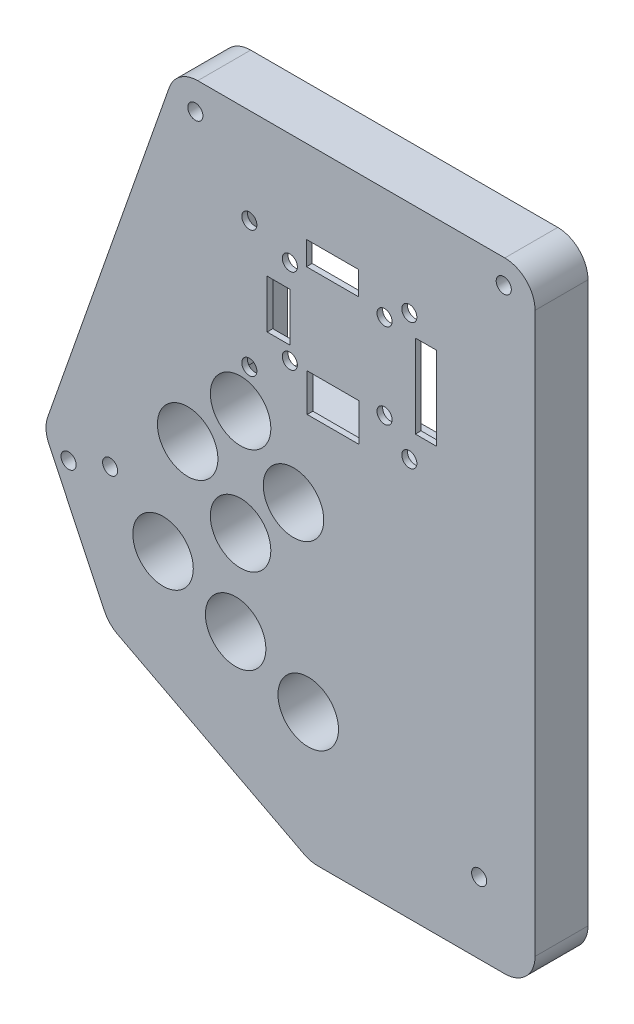
SolidWorks part; units mm, degrees
ref_plane "Front Plane" through (0, 0, 0) normal (0, 0, 1) x (1, 0, 0)
ref_plane "Top Plane" through (0, 0, 0) normal (0, 1, 0) x (1, 0, 0)
ref_plane "Right Plane" through (0, 0, 0) normal (1, 0, 0) x (0, 0, -1)
sketch "Sketch1" plane through (0, 0, 0) normal (0, 0, 1) x (1, 0, 0)
  line L6 (-20.066, -57.15) -> (46.99, -57.15) construction
  line L7 (-12.446, -73.152) -> (46.99, -73.152) construction
  line L8 (-3.3141, 6.35) -> (48.26, 6.35)
  line L9 (53.34, 1.27) -> (53.34, -92.71)
  line L10 (48.26, -97.79) -> (16.847, -97.79)
  line L16 (-8.1072, 2.9529) -> (-28.5162, -55.1739)
  line L18 (-20.066, -57.15) -> (-29.21, -57.15) construction
  line L26 (0, 0) -> (46.99, 0) construction
  line L27 (46.99, 0) -> (46.99, -88.9) construction
  line L28 (46.99, -88.9) -> (17.78, -88.9) construction
  line L29 (17.78, -88.9) -> (-12.446, -73.152) construction
  line L30 (-12.446, -73.152) -> (-20.066, -57.15) construction
  line L31 (-20.066, -57.15) -> (0, 0) construction
  line L32 (46.99, -57.15) -> (46.99, -88.9) construction
  line L33 (17.78, -88.9) -> (15.603, -97.79) construction
  line L34 (-12.446, -73.152) -> (-17.9301, -78.4424) construction
  line L35 (14.4997, -97.2152) -> (-16.7505, -80.9336)
  line L36 (-28.3096, -59.0409) -> (-18.9898, -78.6124)
  arc A0 (53.34, -92.71) -> (48.26, -97.79) centre (48.26, -92.71) cw
  arc A1 (48.26, 6.35) -> (53.34, 1.27) centre (48.26, 1.27) cw
  arc A2 (-8.1072, 2.9529) -> (-3.3141, 6.35) centre (-3.3141, 1.27) cw
  arc A3 (14.4997, -97.2152) -> (16.847, -97.79) centre (16.847, -92.71) ccw
  arc A4 (-16.7505, -80.9336) -> (-18.9898, -78.6124) centre (-14.4033, -76.4284) cw
  arc A5 (-28.5162, -55.1739) -> (-28.3096, -59.0409) centre (-23.723, -56.8568) ccw
  point P16 (53.34, -97.79)
  point P20 (53.34, 6.35)
  dimension "D8" = 5.08
  dimension "D9" = 5.08
  dimension "D1" = 88.9
  dimension "D2" = 29.21
  dimension "D3" = 59.436
  dimension "D4" = 67.056
  dimension "D5" = 104.14
  dimension "D6" = 82.55
  dimension "D7" = 46.99
  dimension "D13" = 103.76
  dimension "D17" = 108.51
extrude "Boss-Extrude1" add sketch "Sketch1" along normal blind 8.89
sketch "Sketch3" plane through (0, 0, 8.89) normal (0, 0, 1) x (1, 0, 0)
  line L6 (-20.066, -57.15) -> (46.99, -57.15) construction
  line L7 (-12.446, -73.152) -> (46.99, -73.152) construction
  line L8 (0, 0) -> (46.99, 0) construction
  line L9 (46.99, 0) -> (46.99, -88.9) construction
  line L10 (46.99, -88.9) -> (17.78, -88.9) construction
  line L11 (17.78, -88.9) -> (-12.446, -73.152) construction
  line L12 (-12.446, -73.152) -> (-20.066, -57.15) construction
  line L13 (-20.066, -57.15) -> (0, 0) construction
  line L14 (3.8784, -55.88) -> (3.8784, -38.1) construction
  circle A0 centre (3.8784, -38.1) radius 5.08
  circle A1 centre (-5.0116, -46.99) radius 5.08
  circle A2 centre (3.8784, -55.88) radius 5.08
  circle A3 centre (12.7684, -46.99) radius 5.08
  circle A4 centre (-9.144, -65.024) radius 5.08
  circle A5 centre (3.048, -70.612) radius 5.08
  circle A6 centre (15.24, -76.2) radius 5.08
  dimension "D7" = 10.16
  dimension "D1" = 43.1116
  dimension "D2" = 8.89
  dimension "D3" = 8.89
  dimension "D4" = 46.99
  dimension "D5" = 8.89
  dimension "D6" = 8.89
  dimension "D8" = 12.192
  dimension "D9" = 5.588
  dimension "D10" = 5.588
  dimension "D11" = 12.192
  dimension "D12" = 43.942
  dimension "D13" = 70.612
sketch "Sketch4" plane through (0, 0, 0) normal (0, 0, 1) x (1, 0, 0)
  line L0 (2.8795, -3.175) -> (2.8795, -33.655)
  line L6 (2.8795, -3.175) -> (37.1695, -3.175)
  line L9 (37.1695, -3.175) -> (37.1695, -33.655)
  line L48 (37.1695, -33.655) -> (2.8795, -33.655)
  line L50 (46.99, 0) -> (46.99, -88.9) construction
  dimension "D1" = 9.8205
  dimension "D2" = 34.29
  dimension "D3" = 30.48
sketch "Sketch9" plane through (0, 0, 0) normal (0, 0, -1) x (-1, 0, 0)
  line L0 (-46.99, 0) -> (-46.99, -88.9) construction
  line L7 (-36.7885, -35.5217) -> (-36.7885, -40.4326) construction
  line L8 (-53.34, -92.71) -> (-53.34, 1.27) construction
  line L9 (-48.26, 6.35) -> (3.3141, 6.35) construction
  line L10 (3.3141, 6.35) -> (-48.26, 6.35) construction
  line L11 (-53.34, 1.27) -> (-53.34, -92.71) construction
  line L25 (-3.2605, -20.3148) -> (-36.7885, -20.3148) construction
  line L26 (-33.4865, -32.221) -> (-29.908, -32.221) construction
  line L27 (-33.4865, -33.0148) -> (-33.4865, -29.5416) construction
  line L28 (-4.0809, -8.4085) -> (-4.0809, -11.8133) construction
  line L29 (-4.0809, -8.4085) -> (-9.1758, -8.4085) construction
  line L30 (-5.0385, -17.1398) -> (-5.005, -17.1398) construction
  line L31 (-5.0385, -7.6148) -> (-5.0652, -7.6148) construction
  line L32 (-8.3409, -24.3788) -> (-8.3409, -16.2508)
  line L33 (-15.0648, -33.0148) -> (-23.8027, -33.0148)
  line L34 (-36.7885, -26.7831) -> (-33.2325, -26.7831)
  line L35 (-36.7885, -12.8131) -> (-36.7885, -26.7831)
  line L36 (-14.9445, -7.6148) -> (-23.6757, -7.6148)
  line L37 (-23.6757, -7.6148) -> (-23.6757, -11.5835)
  line L38 (-15.0648, -33.0148) -> (-15.0648, -26.6648)
  line L39 (-23.8027, -26.6648) -> (-23.8027, -33.0148)
  line L40 (-12.1509, -24.3788) -> (-8.3409, -24.3788)
  line L41 (-8.3409, -16.2508) -> (-12.1509, -16.2508)
  line L42 (-33.2325, -12.8131) -> (-36.7885, -12.8131)
  line L43 (-12.1509, -16.2508) -> (-12.1509, -24.3788)
  line L44 (-14.9445, -11.5835) -> (-23.6757, -11.5835)
  line L45 (-14.9445, -7.6148) -> (-14.9445, -11.5835)
  line L46 (-23.8027, -26.6648) -> (-20.9135, -26.6648)
  line L47 (-15.0648, -26.6648) -> (-20.9135, -26.6648)
  line L48 (-33.2325, -12.8131) -> (-33.2325, -26.7831)
  circle A8 centre (-5.3484, -30.9535) radius 1.2675
  circle A9 centre (-32.219, -9.6761) radius 1.2675
  circle A10 centre (-12.1505, -12.3773) radius 1.2675
  circle A11 centre (-12.1505, -26.6648) radius 1.2675
  circle A12 centre (-28.0572, -12.3773) radius 1.2675
  circle A13 centre (-5.3484, -9.6761) radius 1.2675
  circle A14 centre (-32.219, -30.9535) radius 1.2675
  circle A15 centre (-28.0572, -26.6648) radius 1.2675
  dimension "D1" = 2.535
  dimension "D2" = 10.2015
  dimension "D3" = 16.5515
  dimension "D4" = 19.1631
  dimension "D5" = 13.97
  dimension "D6" = 16.0261
  dimension "D7" = 21.121
extrude "Cut-Extrude6" cut sketch "Sketch9" against normal through all both and the other way through all
extrude "Cut-Extrude7" cut sketch "Sketch4" along normal blind 7.9375 and the other way through all
extrude "Cut-Extrude8" cut sketch "Sketch3" against normal through all both and the other way through all
sketch "Sketch12" plane through (0, 0, 0) normal (0, 0, -1) x (-1, 0, 0)
  line L0 (-48.26, 6.35) -> (3.3141, 6.35) construction
  line L1 (-53.34, -92.71) -> (-53.34, 1.27) construction
  line L2 (8.1072, 2.9529) -> (28.5162, -55.1739) construction
  line L3 (28.3096, -59.0409) -> (18.9898, -78.6124) construction
  circle A0 centre (-48.0822, 2.286) radius 1.27
  circle A1 centre (3.7187, 1.651) radius 1.27
  circle A2 centre (25.0123, -59.762) radius 1.27
  dimension "D1" = 2.54
  dimension "D2" = 4.064
  dimension "D3" = 5.2578
  dimension "D4" = 4.699
  dimension "D5" = 4.572
  dimension "D6" = 4.826
  dimension "D7" = 2.667
extrude "Cut-Extrude9" cut sketch "Sketch12" against normal through all both and the other way through all
sketch "Sketch15" plane through (0, 0, 0) normal (0, 0, -1) x (-1, 0, 0)
  line L0 (-37.465, -31.4407) -> (-43.942, -85.852) construction
  line L1 (20.066, -57.15) -> (18.034, -57.15) construction
  line L2 (20.066, -57.15) -> (-46.99, -57.15) construction
  circle A0 centre (18.034, -57.15) radius 1.27
  circle A1 centre (-43.942, -85.852) radius 1.27
  dimension "D1" = 2.54
  dimension "D2" = 2.032
  dimension "D3" = 54.7954
extrude "Cut-Extrude10" cut sketch "Sketch15" against normal through all both and the other way through all
